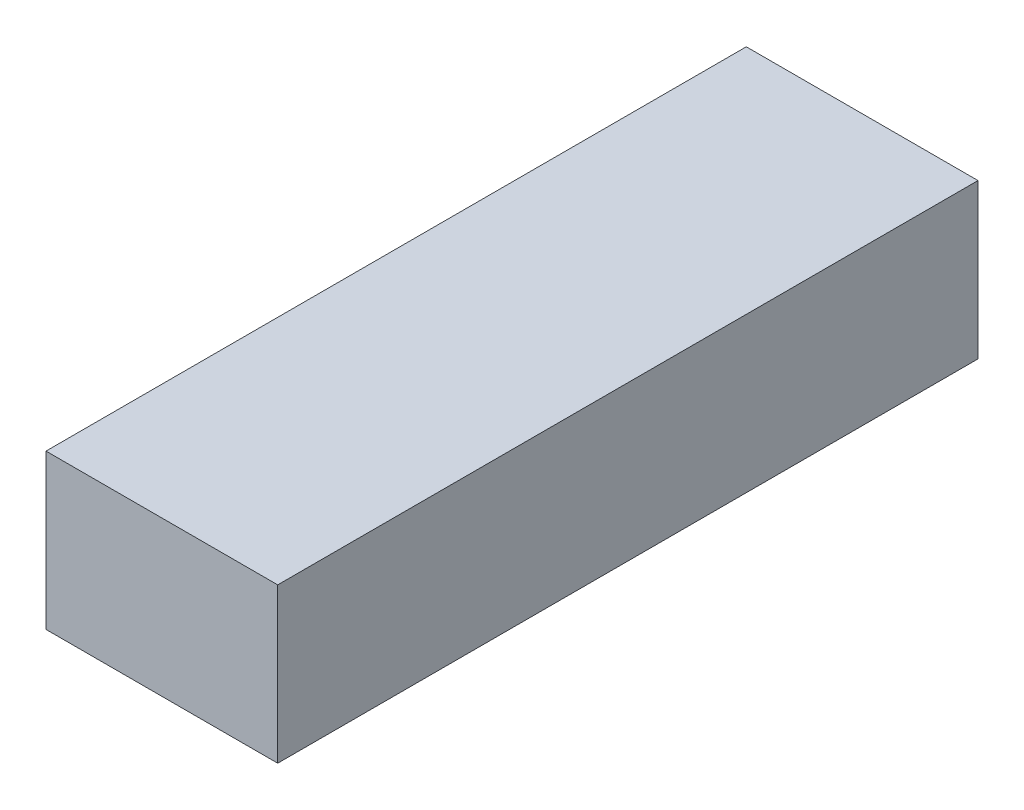
SolidWorks part; units mm, degrees
material "Sheet Moulding Compound"
ref_plane "Front Plane" through (0, 0, 0) normal (0, 0, 1) x (1, 0, 0)
ref_plane "Top Plane" through (0, 0, 0) normal (0, 1, 0) x (1, 0, 0)
ref_plane "Right Plane" through (0, 0, 0) normal (1, 0, 0) x (0, 0, -1)
sketch "Sketch1" plane through (0, 0, 0) normal (0, 0, 1) x (1, 0, 0)
  line L1 (-22.5, -15) -> (22.5, -15)
  line L2 (-22.5, -15) -> (-22.5, 15)
  line L3 (-22.5, 15) -> (22.5, 15)
  line L4 (22.5, -15) -> (22.5, 15)
  line L5 (-22.5, -15) -> (22.5, 15) construction
  line L6 (-22.5, 15) -> (22.5, -15) construction
  point P0 (0, 0)
  dimension "D1" = 45
  dimension "D2" = 30
extrude "Boss-Extrude1" add sketch "Sketch1" along normal blind 136
